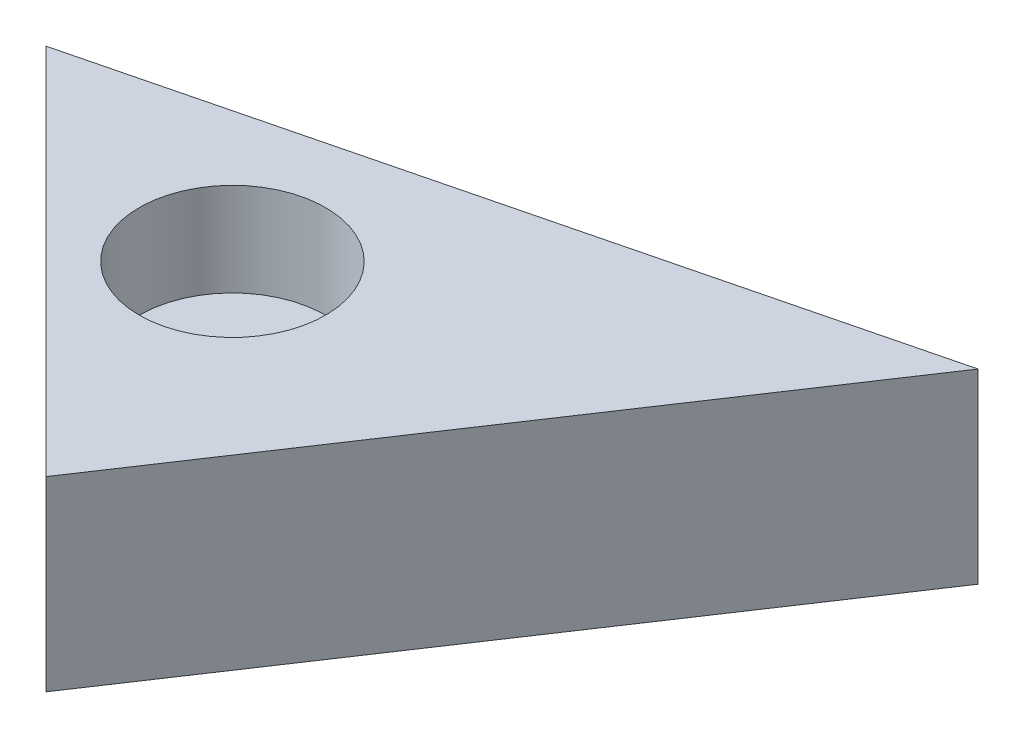
SolidWorks part; units mm, degrees
ref_plane "Front Plane" through (0, 0, 0) normal (0, 0, 1) x (1, 0, 0)
ref_plane "Top Plane" through (0, 0, 0) normal (0, 1, 0) x (1, 0, 0)
ref_plane "Right Plane" through (0, 0, 0) normal (1, 0, 0) x (0, 0, -1)
sketch "Sketch1" plane through (0, 0, 0) normal (0, 1, 0) x (1, 0, 0)
  line L0 (0, 0) -> (50.8, -50.8)
  line L1 (50.8, -50.8) -> (101.6, 25.4)
  line L2 (101.6, 25.4) -> (0, 0)
  dimension "D1" = 50.8
  dimension "D2" = 50.8
  dimension "D3" = 101.6
  dimension "D4" = 25.4
extrude "Boss-Extrude1" add sketch "Sketch1" along normal blind 25.4
sketch "Sketch2" plane through (0, 25.4, 0) normal (0, 1, 0) x (1, 0, 0)
  circle A0 centre (38.1, -12.7) radius 12.7
  dimension "D1" = 25.4
  dimension "D2" = 38.1
  dimension "D3" = 12.7
extrude "Cut-Extrude1" cut sketch "Sketch2" against normal blind 12.7
